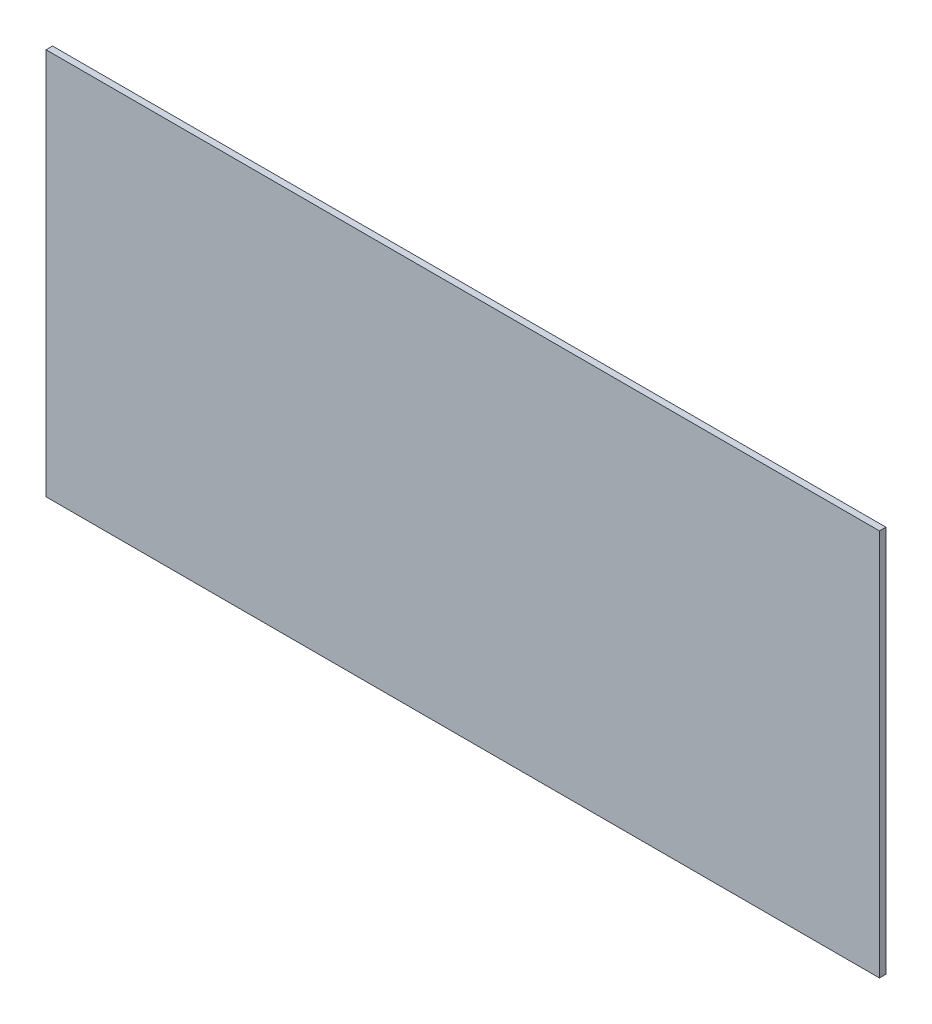
SolidWorks part; units mm, degrees
material "Acrylic (Medium-high impact)"
ref_plane "Front Plane" through (0, 0, 0) normal (0, 0, 1) x (1, 0, 0)
ref_plane "Top Plane" through (0, 0, 0) normal (0, 1, 0) x (1, 0, 0)
ref_plane "Right Plane" through (0, 0, 0) normal (1, 0, 0) x (0, 0, -1)
sketch "Sketch1" plane through (0, 0, 0) normal (0, 0, 1) x (1, 0, 0)
  line L1 (-289.5, -134.5) -> (289.5, -134.5)
  line L2 (-289.5, -134.5) -> (-289.5, 134.5)
  line L3 (-289.5, 134.5) -> (289.5, 134.5)
  line L4 (289.5, -134.5) -> (289.5, 134.5)
  line L5 (-289.5, -134.5) -> (289.5, 134.5) construction
  line L6 (-289.5, 134.5) -> (289.5, -134.5) construction
  point P0 (0, 0)
  dimension "D1" = 579
  dimension "D2" = 269
extrude "Boss-Extrude1" add sketch "Sketch1" along normal mid plane 4.4958
